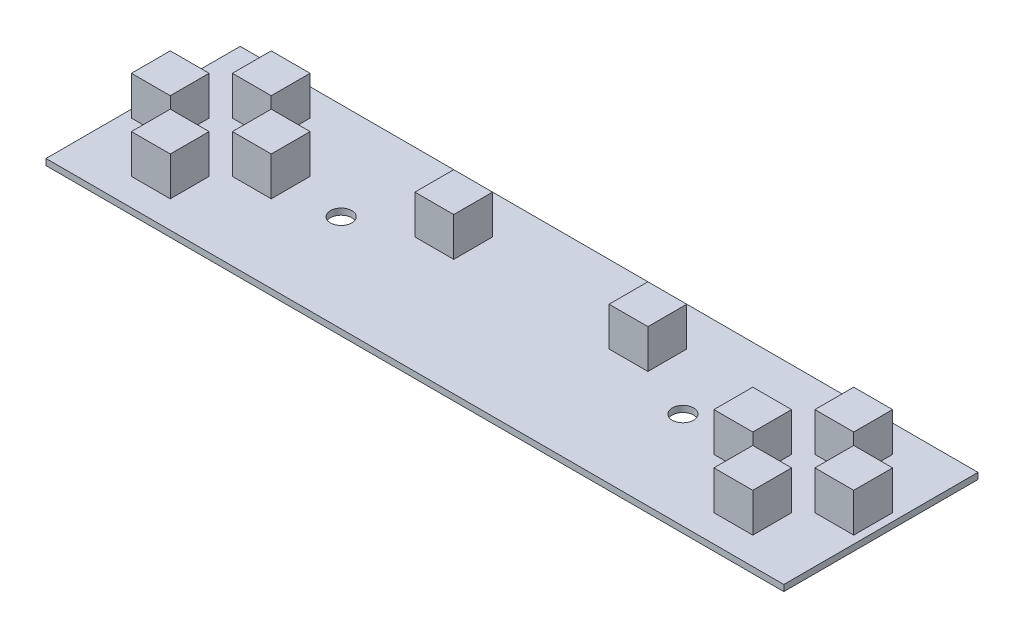
SolidWorks part; units mm, degrees
ref_plane "Front Plane" through (0, 0, 0) normal (0, 0, 1) x (1, 0, 0)
ref_plane "Top Plane" through (0, 0, 0) normal (0, 1, 0) x (1, 0, 0)
ref_plane "Right Plane" through (0, 0, 0) normal (1, 0, 0) x (0, 0, -1)
sketch "Sketch1" plane through (0, 0, 0) normal (0, 1, 0) x (1, 0, 0)
  line L1 (95, -25) -> (-95, -25)
  line L2 (95, -25) -> (95, 25)
  line L3 (95, 25) -> (-95, 25)
  line L4 (-95, -25) -> (-95, 25)
  line L5 (95, -25) -> (-95, 25) construction
  line L6 (95, 25) -> (-95, -25) construction
  point P0 (0, 0)
  dimension "D1" = 50
  dimension "D2" = 190
extrude "Base" add sketch "Sketch1" along normal mid plane 1.6
sketch "Sketch2" plane through (0, 0.8, 0) normal (0, 1, 0) x (1, 0, 0)
  line L0 (0, 0) -> (0, 25) construction
  line L1 (95, 25) -> (-95, 25) construction
  line L2 (-67, -5) -> (-57, -5)
  line L3 (-80, 8) -> (-70, 8)
  line L4 (-80, 8) -> (-80, 18)
  line L5 (-80, 18) -> (-70, 18)
  line L6 (-70, 8) -> (-70, 18)
  line L7 (-80, 8) -> (-70, 18) construction
  line L8 (-80, 18) -> (-70, 8) construction
  line L9 (-57, 5) -> (-57, -5)
  line L10 (-67, 5) -> (-57, 5)
  line L11 (-67, 5) -> (-67, -5)
  line L12 (-80, -8) -> (-80, -18)
  line L13 (-70, -18) -> (-80, -18)
  line L14 (-70, -8) -> (-70, -18)
  line L15 (-70, -8) -> (-80, -8)
  line L16 (-83, 5) -> (-93, 5)
  line L17 (-93, -5) -> (-93, 5)
  line L18 (-83, -5) -> (-93, -5)
  line L19 (-83, -5) -> (-83, 5)
  line L20 (20, 15) -> (30, 5) construction
  line L21 (-20, 5) -> (-30, 5)
  line L22 (-20, 5) -> (-20, 15)
  line L23 (-20, 15) -> (-30, 15)
  line L24 (-30, 5) -> (-30, 15)
  line L25 (-20, 5) -> (-30, 15) construction
  line L26 (-20, 15) -> (-30, 5) construction
  line L27 (20, 5) -> (30, 15) construction
  line L28 (80, 18) -> (70, 8) construction
  line L29 (80, 8) -> (70, 18) construction
  line L30 (30, 5) -> (30, 15)
  line L31 (20, 15) -> (30, 15)
  line L32 (20, 5) -> (20, 15)
  line L33 (20, 5) -> (30, 5)
  line L34 (83, -5) -> (83, 5)
  line L35 (83, -5) -> (93, -5)
  line L36 (93, -5) -> (93, 5)
  line L37 (83, 5) -> (93, 5)
  line L38 (70, -8) -> (80, -8)
  line L39 (70, -8) -> (70, -18)
  line L40 (70, -18) -> (80, -18)
  line L41 (80, -8) -> (80, -18)
  line L42 (67, 5) -> (67, -5)
  line L43 (67, 5) -> (57, 5)
  line L44 (57, 5) -> (57, -5)
  line L45 (70, 8) -> (70, 18)
  line L46 (80, 18) -> (70, 18)
  line L47 (80, 8) -> (80, 18)
  line L48 (80, 8) -> (70, 8)
  line L49 (67, -5) -> (57, -5)
  circle A0 centre (-75, 0) radius 13 construction
  circle A1 centre (75, 0) radius 13 construction
  point P7 (0, 0)
  point P9 (-75, 13)
  point P14 (-25, 10)
  point P27 (-75, 0)
  point P53 (25, 10)
  point P54 (75, 13)
  point P55 (0, 0)
  point P56 (-23.6846, 8)
  dimension "D1" = 26
  dimension "D2" = 75
  dimension "D3" = 10
  dimension "D4" = 10
  dimension "D6" = 10
  dimension "D7" = 25
  dimension "D5" = 4
extrude "Switches" add sketch "Sketch2" along normal blind 10
hole_wizard "M5 Clearance Hole1" positions "Sketch3" profile "Sketch4" hole size "M5" standard "ANSI Metric" end condition through all
sketch "Sketch3" plane through (0, 0.8, 0) normal (0, 1, 0) x (1, 0, 0)
  line L0 (0, 0) -> (0, 25) construction
  line L1 (95, 25) -> (-95, 25) construction
  point P0 (-44, 0)
  point P10 (44, 0)
  dimension "D1" = 44
sketch "Sketch4" plane through (-44, 0.8, 0) normal (1, 0, 0) x (0, 0, 1)
  line L0 (0, 0) -> (0, 1.6)
  line L1 (0, 1.6) -> (2.75, 1.6)
  line L2 (2.75, 1.6) -> (2.75, 0)
  line L5 (2.75, 0) -> (0, 0)
  line L11 (0, -6.35) -> (0, 107.95) construction
  dimension "Thru Hole Dia." = 5.5
  dimension "Thru Hole Depth" = 1.6
